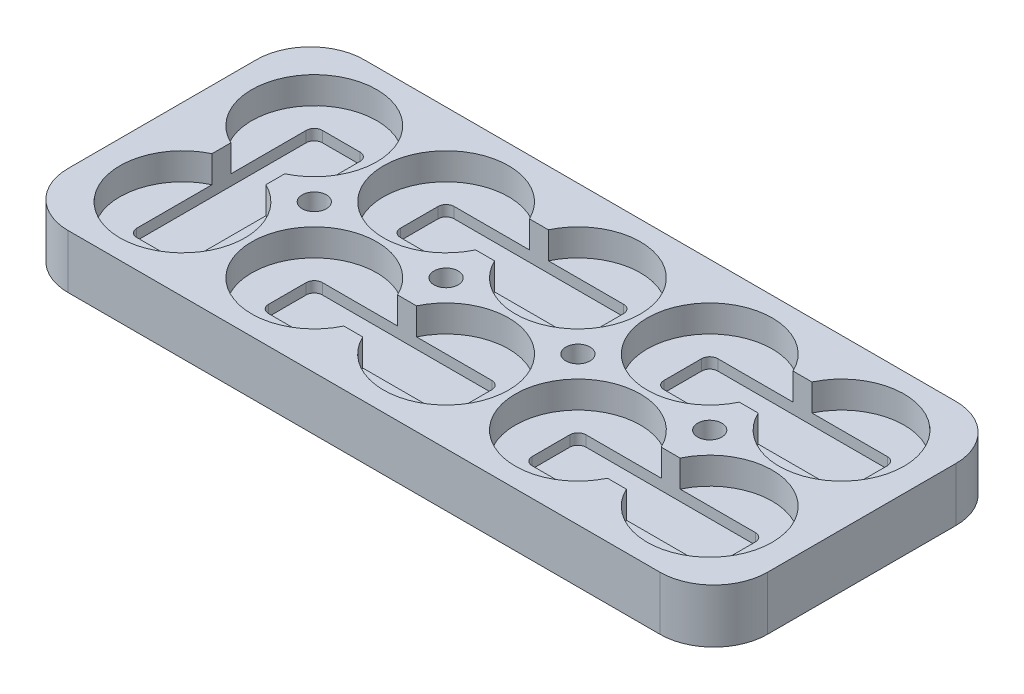
SolidWorks part; units mm, degrees
material "ABS"
ref_plane "Ebene vorne" through (0, 0, 0) normal (0, 0, 1) x (1, 0, 0)
ref_plane "Ebene oben" through (0, 0, 0) normal (0, 1, 0) x (1, 0, 0)
ref_plane "Ebene rechts" through (0, 0, 0) normal (1, 0, 0) x (0, 0, -1)
sketch "Skizze1" plane through (0, 0, 0) normal (0, 1, 0) x (1, 0, 0)
  line L1 (0, 0) -> (130, 0)
  line L2 (0, 0) -> (0, 55)
  line L3 (0, 55) -> (130, 55)
  line L4 (130, 0) -> (130, 55)
  dimension "D1" = 55
  dimension "D2" = 130
extrude "Aufsatz-Linear austragen1" add sketch "Skizze1" along normal blind 10
fillet "Verrundung1" radius 10 4 edges at (130, 5, 0) (130, 5, -55) (0, 5, -55) (0, 5, 0)
hole_wizard "Durchgangsloch für M41" positions "Skizze7" profile "Skizze6" hole size "M4" standard "DIN" end condition through all
sketch "Skizze7" plane through (0, 0, 0) normal (0, -1, 0) x (-1, 0, 0)
  line L0 (0, 27.5) -> (-28.25, 27.5)
  line L1 (0, 45) -> (0, 10) construction
  line L2 (-28.25, 27.5) -> (-52.75, 27.5)
  line L3 (-52.75, 27.5) -> (-77.25, 27.5)
  line L4 (-77.25, 27.5) -> (-101.75, 27.5)
  line L5 (-101.75, 27.5) -> (-130, 27.5)
  line L6 (-130, 10) -> (-130, 45) construction
  point P2 (-77.25, 27.5)
  point P6 (-52.75, 27.5)
  point P8 (-28.25, 27.5)
  point P31 (-101.75, 27.5)
  dimension "D1" = 24.5
sketch "Skizze6" plane through (77.25, 0, -27.5) normal (1, 0, 0) x (0, 0, -1)
  line L0 (0, 0) -> (0, 10)
  line L1 (0, 10) -> (2.25, 10)
  line L2 (2.25, 10) -> (2.25, 0)
  line L5 (2.25, 0) -> (0, 0)
  line L11 (0, -6.35) -> (0, 107.95) construction
  dimension "Bohrerdurchmesser" = 4.5
  dimension "Bohrungstiefe" = 10
sketch "Skizze3" plane through (0, 10, 0) normal (0, 1, 0) x (1, 0, 0)
  line L0 (16, 15.25) -> (16, 39.75) construction
  line L1 (16, 15.25) -> (114, 15.25) construction
  line L2 (65, 15.25) -> (65, 0) construction
  line L3 (10, 0) -> (120, 0) construction
  line L4 (0, 27.5) -> (16, 27.5) construction
  line L5 (0, 45) -> (0, 10) construction
  circle A0 centre (16, 15.25) radius 11.625
  circle A1 centre (40.5, 15.25) radius 11.625
  circle A2 centre (65, 15.25) radius 11.625
  circle A3 centre (89.5, 15.25) radius 11.625
  circle A4 centre (114, 15.25) radius 11.625
  circle A5 centre (40.5, 39.75) radius 11.625
  circle A6 centre (65, 39.75) radius 11.625
  circle A7 centre (89.5, 39.75) radius 11.625
  circle A8 centre (114, 39.75) radius 11.625
  circle A9 centre (16, 39.75) radius 11.625
  dimension "D1" = 23.25
  dimension "D4" = 24.5
  dimension "D5" = 24.5
  dimension "D2" = 5
  dimension "D3" = 2
extrude "Schnitt-Linear austragen1" cut sketch "Skizze3" against normal blind 5
sketch "Skizze4" plane through (0, 5, 0) normal (0, 1, 0) x (1, 0, 0)
  line L1 (109, 20.25) -> (143.5, 20.25)
  line L2 (109, 20.25) -> (109, 10.25)
  line L3 (109, 10.25) -> (143.5, 10.25)
  line L4 (143.5, 20.25) -> (143.5, 10.25)
  line L5 (94.5, 10.25) -> (60, 10.25)
  line L6 (94.5, 10.25) -> (94.5, 20.25)
  line L7 (94.5, 20.25) -> (60, 20.25)
  line L8 (60, 10.25) -> (60, 20.25)
  line L9 (45.5, 10.25) -> (11, 10.25)
  line L10 (45.5, 10.25) -> (45.5, 20.25)
  line L11 (45.5, 20.25) -> (11, 20.25)
  line L12 (11, 10.25) -> (11, 20.25)
  line L13 (11, 44.75) -> (45.5, 44.75)
  line L14 (11, 44.75) -> (11, 34.75)
  line L15 (11, 34.75) -> (45.5, 34.75)
  line L16 (45.5, 44.75) -> (45.5, 34.75)
  line L17 (60, 44.75) -> (94.5, 44.75)
  line L18 (60, 44.75) -> (60, 34.75)
  line L19 (60, 34.75) -> (94.5, 34.75)
  line L20 (94.5, 44.75) -> (94.5, 34.75)
  line L21 (109, 44.75) -> (143.5, 44.75)
  line L22 (109, 44.75) -> (109, 34.75)
  line L23 (109, 34.75) -> (143.5, 34.75)
  line L24 (143.5, 44.75) -> (143.5, 34.75)
  circle A0 centre (16, 15.25) radius 5 construction
  circle A1 centre (16, 15.25) radius 11.625 construction
  circle A2 centre (40.5, 15.25) radius 5 construction
  circle A3 centre (65, 15.25) radius 5 construction
  circle A4 centre (89.5, 15.25) radius 5 construction
  circle A5 centre (114, 15.25) radius 5 construction
  circle A6 centre (40.5, 15.25) radius 11.625 construction
  circle A7 centre (65, 15.25) radius 11.625 construction
  circle A8 centre (89.5, 15.25) radius 11.625 construction
  circle A9 centre (114, 15.25) radius 11.625 construction
  circle A10 centre (16, 39.75) radius 5 construction
  circle A11 centre (16, 39.75) radius 11.625 construction
  dimension "D1" = 10
extrude "Schnitt-Linear austragen2" [suppressed] cut sketch "Skizze4" against normal blind 2 and the other way up to next
fillet "Verrundung2" [suppressed] radius 2
sketch "Skizze8" plane through (0, 5, 0) normal (0, 1, 0) x (1, 0, 0)
  line L1 (119, 44.75) -> (84.5, 44.75)
  line L2 (119, 44.75) -> (119, 34.75)
  line L3 (119, 34.75) -> (84.5, 34.75)
  line L4 (84.5, 44.75) -> (84.5, 34.75)
  line L5 (119, 20.25) -> (84.5, 20.25)
  line L6 (119, 20.25) -> (119, 10.25)
  line L7 (119, 10.25) -> (84.5, 10.25)
  line L8 (84.5, 20.25) -> (84.5, 10.25)
  line L9 (70, 44.75) -> (35.5, 44.75)
  line L10 (70, 44.75) -> (70, 34.75)
  line L11 (70, 34.75) -> (35.5, 34.75)
  line L12 (35.5, 44.75) -> (35.5, 34.75)
  line L13 (70, 20.25) -> (35.5, 20.25)
  line L14 (70, 20.25) -> (70, 10.25)
  line L15 (70, 10.25) -> (35.5, 10.25)
  line L16 (35.5, 20.25) -> (35.5, 10.25)
  line L17 (11, 44.75) -> (21, 44.75)
  line L18 (11, 44.75) -> (11, 10.25)
  line L19 (11, 10.25) -> (21, 10.25)
  line L20 (21, 44.75) -> (21, 10.25)
  circle A0 centre (114, 39.75) radius 5 construction
  circle A3 centre (114, 39.75) radius 11.625 construction
  circle A4 centre (89.5, 39.75) radius 5 construction
  circle A5 centre (65, 39.75) radius 5 construction
  circle A6 centre (40.5, 39.75) radius 5 construction
  circle A7 centre (16, 39.75) radius 5 construction
  circle A8 centre (89.5, 15.25) radius 5 construction
  circle A9 centre (65, 15.25) radius 5 construction
  circle A10 centre (40.5, 15.25) radius 5 construction
  circle A11 centre (16, 15.25) radius 5 construction
  circle A12 centre (114, 15.25) radius 5 construction
  circle A13 centre (16, 15.25) radius 11.625 construction
  circle A14 centre (114, 15.25) radius 11.625 construction
  dimension "D1" = 10
  dimension "D2" = 5
  dimension "D3" = 2
extrude "Schnitt-Linear austragen3" cut sketch "Skizze8" against normal blind 2 and the other way up to next
fillet "Verrundung3" radius 1.5 20 edges at (21, 4, -44.75) (70, 4, -20.25) (70, 4, -44.75) (119, 4, -44.75) (119, 4, -20.25) (11, 4, -10.25) (35.5, 4, -34.75) (84.5, 4, -34.75) (84.5, 4, -10.25) (35.5, 4, -10.25) (21, 4, -10.25) (70, 4, -34.75) (70, 4, -10.25) (119, 4, -34.75) (119, 4, -10.25) (35.5, 4, -20.25) (84.5, 4, -20.25) (84.5, 4, -44.75) (35.5, 4, -44.75) (11, 4, -44.75)
